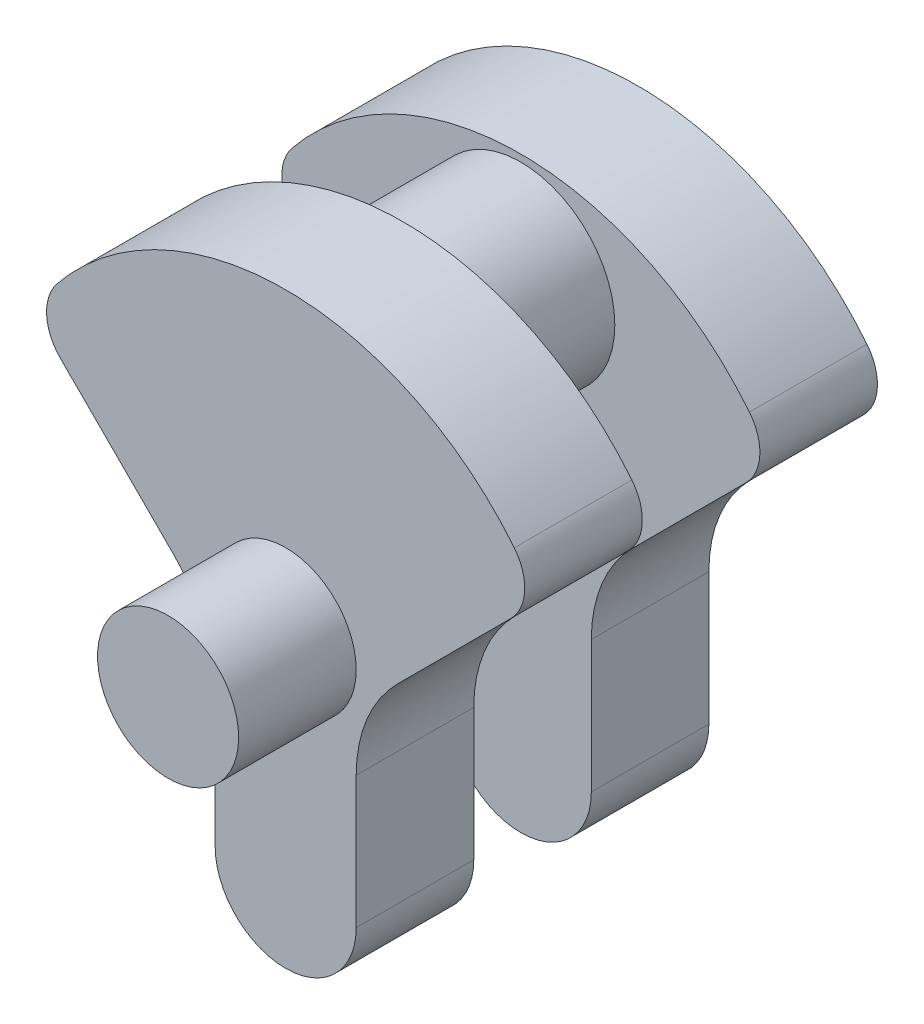
SolidWorks part; units mm, degrees
ref_plane "Front" through (0, 0, 0) normal (0, 0, 1) x (1, 0, 0)
ref_plane "Top" through (0, 0, 0) normal (0, 1, 0) x (1, 0, 0)
ref_plane "Right" through (0, 0, 0) normal (1, 0, 0) x (0, 0, -1)
sketch "Sketch1" plane through (0, 0, 0) normal (0, 0, 1) x (1, 0, 0)
  line L0 (0, 0) -> (0, -62.5) construction
  line L1 (-15, 0) -> (-15, -62.5)
  line L2 (15, 0) -> (15, -62.5)
  line L3 (-53.8033, 31.8033) -> (-15, -7)
  line L4 (15, -7) -> (53.8033, 31.8033)
  circle A0 centre (0, 0) radius 62.5
  circle A1 centre (0, -47.5) radius 15
  dimension "D1" = 125
  dimension "D2" = 15
  dimension "D4" = 90
  dimension "D5" = 7
  dimension "D3" = 15
sketch "Sketch2" plane through (0, 0, 0) normal (0, 0, 1) x (1, 0, 0)
  line L0 (15, -7) -> (53.8033, 31.8033) construction
  line L1 (-53.8033, 31.8033) -> (-15, -7) construction
  line L2 (15, 0) -> (15, -62.5) construction
  line L3 (-15, 0) -> (-15, -62.5) construction
  line L4 (15, -7) -> (53.8033, 31.8033)
  line L5 (-53.8033, 31.8033) -> (-15, -7)
  line L6 (15, -7) -> (15, -47.5)
  line L7 (-15, -7) -> (-15, -47.5)
  line L8 (-15, -60.6733) -> (-15, -62.5)
  line L9 (15, -60.6733) -> (15, -62.5)
  circle A1 centre (0, -47.5) radius 15
  arc A2 (-15, -47.5) -> (15, -47.5) centre (0, -47.5) ccw
  circle A3 centre (0, 0) radius 62.5
  circle A4 centre (0, 0) radius 62.5
  dimension "D1" = 0
  dimension "D2" = 0
extrude "Boss-Extrude1" add sketch "Sketch2" along normal mid plane 75 contours L4 A4 L5 L7 A2 L6
fillet "Fillet1" radius 10 2 edges at (-53.8033, 31.8033, 0) (53.8033, 31.8033, 0)
sketch "Sketch3" plane through (0, 0, 37.5) normal (0, 0, 1) x (1, 0, 0)
  circle A0 centre (0, 41) radius 20
  arc A1 (48.6233, 39.2687) -> (-48.6233, 39.2687) centre (0, 0) ccw construction
  point P2 (0, 14.9839)
  point P4 (0, 0)
  dimension "D1" = 40
  dimension "D2" = 1.5
sketch "Sketch4" plane through (0, 0, 0) normal (1, 0, 0) x (0, 0, -1)
  line L0 (-37.5, 21) -> (122.8392, 21) construction
  line L1 (12.5, 21) -> (-12.5, 21)
  line L2 (12.5, 21) -> (12.5, -84.7076)
  line L3 (12.5, -84.7076) -> (-12.5, -84.7076)
  line L4 (-12.5, 21) -> (-12.5, -84.7076)
  line L8 (-37.5, 41) -> (122.8392, 41)
  point P4 (0, 21)
  dimension "D1" = 25
  dimension "D2" = 20
revolve "Cut-Revolve1" cut sketch "Sketch4" angle 360 about L8
fillet "Fillet2" radius 30 4 edges at (15, -7, -25) (15, -7, 25) (-15, -7, -25) (-15, -7, 25)
sketch "Sketch5" plane through (0, 0, 37.5) normal (0, 0, 1) x (1, 0, 0)
  circle A0 centre (0, 0) radius 15
  dimension "D1" = 30
extrude "Boss-Extrude2" add sketch "Sketch5" along normal blind 25
mirror "Mirror1" about plane through (0, 0, 0) normal (0, 0, 1) of "Boss-Extrude2"
